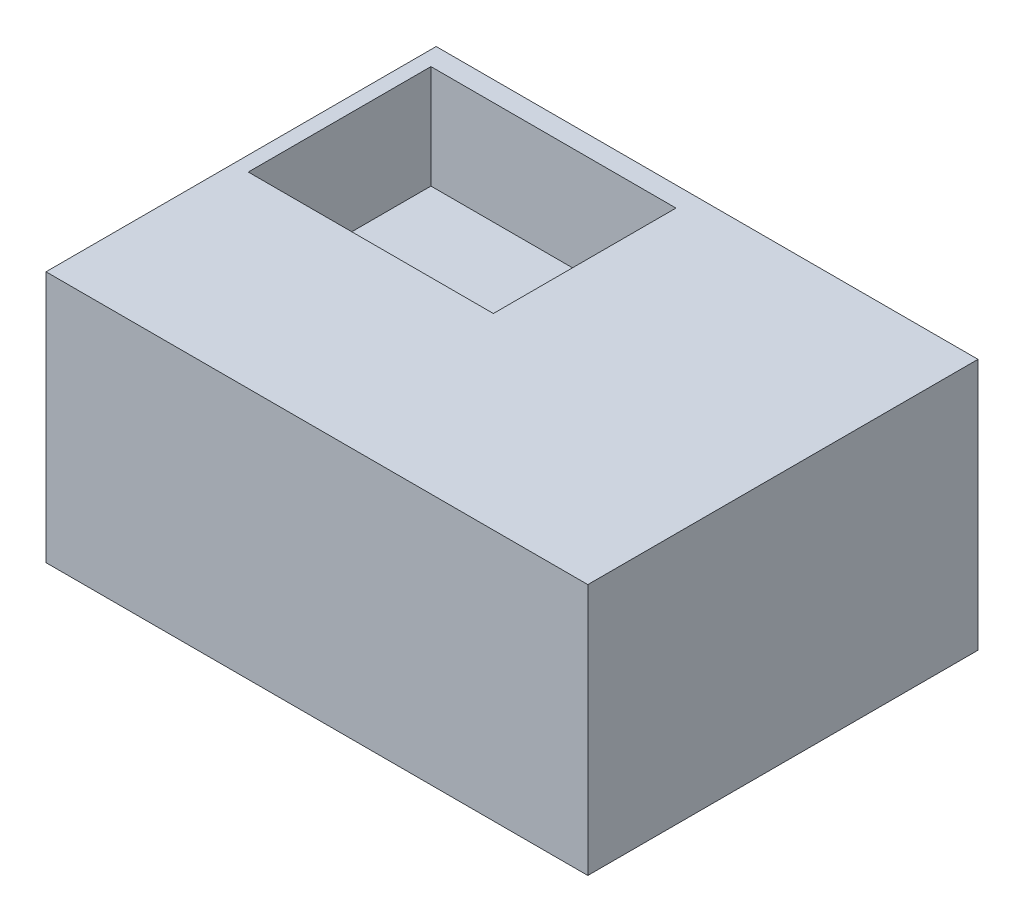
SolidWorks part; units mm, degrees
ref_plane "Front Plane" through (0, 0, 0) normal (0, 0, 1) x (1, 0, 0)
ref_plane "Top Plane" through (0, 0, 0) normal (0, 1, 0) x (1, 0, 0)
ref_plane "Right Plane" through (0, 0, 0) normal (1, 0, 0) x (0, 0, -1)
sketch "Sketch1" plane through (0, 0, 0) normal (0, 1, 0) x (1, 0, 0)
  line L1 (-57.7554, -43.3639) -> (62.6788, -43.3639)
  line L2 (-57.7554, -43.3639) -> (-57.7554, 43.3639)
  line L3 (-57.7554, 43.3639) -> (62.6788, 43.3639)
  line L4 (62.6788, -43.3639) -> (62.6788, 43.3639)
  line L5 (-57.7554, -43.3639) -> (62.6788, 43.3639) construction
  line L6 (-57.7554, 43.3639) -> (62.6788, -43.3639) construction
  point P0 (2.4617, 0)
extrude "Boss-Extrude1" add sketch "Sketch1" along normal blind 56
sketch "Sketch2" plane through (0, 56, 0) normal (0, 1, 0) x (1, 0, 0)
  line L1 (-54.4714, 38.9125) -> (0, 38.9125)
  line L2 (-54.4714, 38.9125) -> (-54.4714, -1.6832)
  line L3 (-54.4714, -1.6832) -> (0, -1.6832)
  line L4 (0, 38.9125) -> (0, -1.6832)
extrude "Cut-Extrude1" cut sketch "Sketch2" against normal blind 23
sketch3d "3DSketch1"
  line L0 (0, 51, 1.6832) -> (0, 51, -38.9125)
  line L1 (0, 51, 1.6832) -> (0, 51, -38.9125) construction
  line L2 (0, 51, -38.9125) -> (-54.4714, 51, -38.9125)
  line L3 (0, 51, -38.9125) -> (-54.4714, 51, -38.9125) construction
  dimension "D1" = 5
  dimension "D2" = 5
